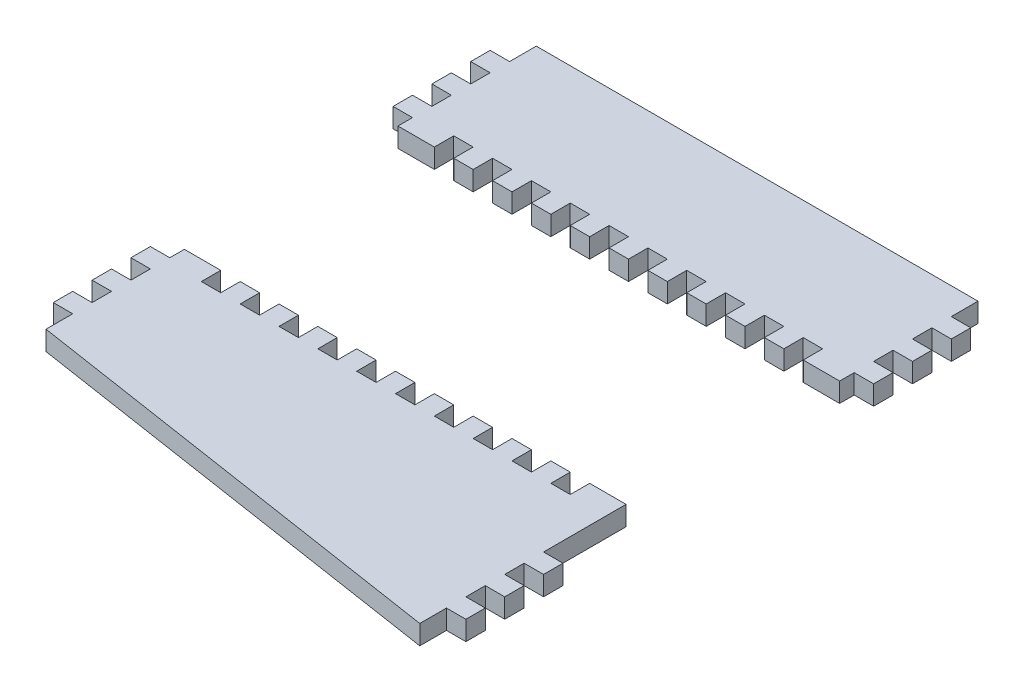
SolidWorks part; units mm, degrees
material "Cedar"
ref_plane "Front Plane" through (0, 0, 0) normal (0, 0, 1) x (1, 0, 0)
ref_plane "Top Plane" through (0, 0, 0) normal (0, 1, 0) x (1, 0, 0)
ref_plane "Right Plane" through (0, 0, 0) normal (1, 0, 0) x (0, 0, -1)
sketch "Sketch1" plane through (0, 0, 0) normal (0, 1, 0) x (1, 0, 0)
  line L0 (-14.4787, 45) -> (-18.4787, 45)
  line L1 (-18.4787, 45) -> (-18.4787, 41)
  line L2 (-18.4787, 41) -> (-14.4787, 41)
  line L3 (-14.4787, 41) -> (-14.4787, 37)
  line L4 (-14.4787, 37) -> (-18.4787, 37)
  line L5 (-18.4787, 37) -> (-18.4787, 33)
  line L6 (-14.4787, 45) -> (-14.4787, 50.5)
  line L7 (-14.4787, 50.5) -> (76.5213, 50.5)
  line L8 (-14.4787, 25) -> (-14.4787, -25)
  line L9 (-14.4787, 33) -> (-18.4787, 33)
  line L10 (-14.4787, 29) -> (-14.4787, 33)
  line L11 (0, 0) -> (-45.8811, 0) construction
  line L12 (-18.4787, 29) -> (-14.4787, 29)
  line L13 (-18.4787, 25) -> (-18.4787, 29)
  line L14 (-14.4787, 25) -> (-18.4787, 25)
  line L15 (-14.4787, 442.2268) -> (-14.4787, 342.2268) construction
  line L16 (-14.4787, 442.2268) -> (1285.5213, 442.2268) construction
  line L17 (-14.4787, 342.2268) -> (1285.5213, 142.2268) construction
  line L18 (1285.5213, 142.2268) -> (1285.5213, 442.2268) construction
  line L19 (-7.4787, 442.2268) -> (-7.4787, 341.1498) construction
  line L20 (96.5213, 442.2268) -> (96.5213, 325.1498) construction
  line L21 (1285.5213, 442.2268) -> (1885.5213, 442.2268) construction
  line L22 (1885.5213, 442.2268) -> (1885.5213, 142.2268) construction
  line L23 (1885.5213, 142.2268) -> (1285.5213, 142.2268) construction
  line L24 (1885.5213, 442.2268) -> (2485.5213, 442.2268) construction
  line L25 (2485.5213, 442.2268) -> (2485.5213, 342.2268) construction
  line L26 (2485.5213, 342.2268) -> (1885.5213, 142.2268) construction
  line L27 (-18.4787, 35) -> (-56.1025, 35) construction
  line L28 (80.5213, 35) -> (126.3703, 35) construction
  line L29 (76.5213, 50.5) -> (76.5213, 45)
  line L30 (76.5213, 45) -> (80.5213, 45)
  line L31 (80.5213, 45) -> (80.5213, 41)
  line L32 (80.5213, 41) -> (76.5213, 41)
  line L33 (76.5213, 41) -> (76.5213, 37)
  line L34 (76.5213, 37) -> (80.5213, 37)
  line L35 (80.5213, 37) -> (80.5213, 33)
  line L36 (80.5213, 33) -> (76.5213, 33)
  line L37 (76.5213, 33) -> (76.5213, 29)
  line L38 (76.5213, 29) -> (80.5213, 29)
  line L39 (80.5213, 29) -> (80.5213, 25)
  line L40 (80.5213, 25) -> (76.5213, 25)
  line L41 (76.5213, 25) -> (76.5213, -39)
  line L42 (10.595, -7) -> (87.8667, -7) construction
  line L43 (-14.4787, -25) -> (-18.4787, -25)
  line L44 (-18.4787, -25) -> (-18.4787, -29)
  line L45 (-18.4787, -29) -> (-14.4787, -29)
  line L46 (-14.4787, -29) -> (-14.4787, -33)
  line L47 (-14.4787, -33) -> (-18.4787, -33)
  line L48 (-14.4787, -45) -> (-14.4787, -50.5)
  line L49 (-18.4787, -37) -> (-18.4787, -33)
  line L50 (-14.4787, -37) -> (-18.4787, -37)
  line L51 (-14.4787, -41) -> (-14.4787, -37)
  line L52 (-18.4787, -41) -> (-14.4787, -41)
  line L53 (-18.4787, -45) -> (-18.4787, -41)
  line L54 (-14.4787, -45) -> (-18.4787, -45)
  line L55 (80.5213, -39) -> (76.5213, -39)
  line L56 (80.5213, -43) -> (80.5213, -39)
  line L57 (76.5213, -43) -> (80.5213, -43)
  line L58 (76.5213, -47) -> (76.5213, -43)
  line L59 (80.5213, -47) -> (76.5213, -47)
  line L60 (80.5213, -51) -> (80.5213, -47)
  line L61 (76.5213, -51) -> (80.5213, -51)
  line L62 (76.5213, -55) -> (76.5213, -51)
  line L63 (80.5213, -55) -> (76.5213, -55)
  line L64 (80.5213, -59) -> (80.5213, -55)
  line L65 (76.5213, -59) -> (80.5213, -59)
  line L66 (76.5213, -64.5) -> (76.5213, -59)
  line L67 (-14.4787, -50.5) -> (76.5213, -64.5)
  line L68 (290.5213, 442.2268) -> (290.5213, 295.3037) construction
  line L69 (615.5213, 442.2268) -> (615.5213, 245.3037) construction
  line L70 (935.5213, 442.2268) -> (935.5213, 196.0729) construction
  line L71 (1485.5213, 442.2268) -> (1485.5213, 142.2268) construction
  line L72 (1685.5213, 442.2268) -> (1685.5213, 142.2268) construction
  line L73 (2187.5213, 442.2268) -> (2187.5213, 242.2268) construction
  line L74 (1285.5213, 896.9349) -> (1285.5213, 1196.9349) construction
  line L75 (1285.5213, 1046.9349) -> (-14.4787, 1046.9349) construction
  line L76 (-14.4787, 1046.9349) -> (-14.4787, 1104.4349) construction
  line L77 (-14.4787, 1104.4349) -> (1285.5213, 1196.9349) construction
  line L78 (-14.4787, 1046.9349) -> (-14.4787, 989.4349) construction
  line L79 (-14.4787, 989.4349) -> (1285.5213, 896.9349) construction
  line L80 (96.5213, 1112.333) -> (96.5213, 981.5369) construction
  line L81 (290.5213, 967.733) -> (290.5213, 1126.1369) construction
  line L82 (615.5213, 1149.2619) -> (615.5213, 944.608) construction
  line L83 (935.5213, 921.8388) -> (935.5213, 1172.0311) construction
  line L84 (-3.4787, 442.2268) -> (-3.4787, 340.5345) construction
  line L85 (100.5213, 442.2268) -> (100.5213, 324.5345) construction
  line L86 (294.5213, 442.2268) -> (294.5213, 294.6883) construction
  line L87 (619.5213, 442.2268) -> (619.5213, 244.6883) construction
  line L88 (939.5213, 442.2268) -> (939.5213, 195.4575) construction
  line L89 (1881.5213, 442.2268) -> (1881.5213, 142.2268) construction
  line L90 (1289.5213, 442.2268) -> (1289.5213, 142.2268) construction
  line L91 (1489.5213, 442.2268) -> (1489.5213, 142.2268) construction
  line L92 (1689.5213, 442.2268) -> (1689.5213, 142.2268) construction
  line L93 (1285.5213, 1196.9349) -> (1885.5213, 1196.9349) construction
  line L94 (1885.5213, 1196.9349) -> (1885.5213, 896.9349) construction
  line L95 (1885.5213, 896.9349) -> (1285.5213, 896.9349) construction
  line L96 (1885.5213, 1196.9349) -> (2485.5213, 1052.9349) construction
  line L97 (2485.5213, 1052.9349) -> (2485.5213, 1040.9349) construction
  line L98 (2485.5213, 1040.9349) -> (1885.5213, 896.9349) construction
  line L99 (2191.5213, 1123.4949) -> (2191.5213, 970.3749) construction
  line L100 (2191.5213, 442.2268) -> (2191.5213, 244.2268) construction
  line L101 (2481.5213, 442.2268) -> (2481.5213, 340.8934) construction
  line L102 (-7.4787, 1104.933) -> (-7.4787, 988.9369) construction
  text T0 "Vedere laterala"
  text T1 "vedere laterala" font "Century Gothic" height in points 28
  point P50 (-14.4787, 0)
  point P63 (76.5213, -7)
  dimension "D2" = 4
  dimension "D3" = 4
  dimension "D4" = 4
  dimension "D5" = 4
  dimension "D6" = 91
  dimension "D7" = 100
  dimension "D8" = 346
  dimension "D9" = 300
  dimension "D10" = 115.9962
  dimension "D11" = 7
  dimension "D12" = 100
  dimension "D13" = 4
  dimension "D14" = 290
  dimension "D15" = 101.0769
  dimension "D16" = 117.0769
  dimension "D17" = 35
  dimension "D18" = 50.5
  dimension "D19" = 4
  dimension "D20" = 4
  dimension "D21" = 15.5
  dimension "D22" = 4
  dimension "D23" = 4
  dimension "D24" = 4
  dimension "D25" = 4
  dimension "D26" = 4
  dimension "D27" = 7
  dimension "D28" = 4
  dimension "D29" = 100
  dimension "D30" = 4
  dimension "D31" = 146.9231
  dimension "D32" = 4
  dimension "D33" = 4
  dimension "D34" = 196.9231
  dimension "D35" = 246.1538
  dimension "D36" = 4
  dimension "D37" = 196
  dimension "D38" = 302
  dimension "D39" = 198
  dimension "D40" = 300
  dimension "D41" = 57.5
  dimension "D42" = 57.5
  dimension "D43" = 130.7962
  dimension "D44" = 158.4038
  dimension "D45" = 204.6538
  dimension "D46" = 250.1923
  dimension "D47" = 4
  dimension "D48" = 190
  dimension "D49" = 321
  dimension "D50" = 104
  dimension "D51" = 4
  dimension "D52" = 4
  dimension "D53" = 196
  dimension "D54" = 4
  dimension "D55" = 192
  dimension "D56" = 600
  dimension "D57" = 1300
  dimension "D58" = 6
  dimension "D59" = 6
  dimension "D60" = 4
  dimension "D61" = 4
  dimension "D62" = 600
  dimension "D63" = 300
  dimension "D64" = 153.12
  dimension "D65" = 194
  dimension "D66" = 325
  dimension "D67" = 320
  dimension "D68" = 350
  dimension "D69" = 316
extrude "Boss-Extrude1" add sketch "Sketch1" along normal blind 4 contours L67 L66 L65 L64 L63 L62 L61 L60 L59 L58 L57 L56 L55 L41 L40 L39 L38 L37 L36 L35 L34 L33 L32 L31 L30 L29 L7 L6 L0 L1 L2 L3 L4 L5 L9 L10 L12 L13 L14 L8 L43 L44 L45 L46 L47 L49 L50 L51 L52 L53 L54 L48
sketch "Sketch4" plane through (0, 4, 0) normal (0, 1, 0) x (1, 0, 0)
  line L0 (-34.2055, 0) -> (100.0971, 0) construction
  line L1 (-30.6838, -22) -> (110.8948, -22)
  line L2 (110.8948, -22) -> (110.8948, 22)
  line L3 (110.8948, 22) -> (-30.6838, 22)
  line L4 (-30.6838, 22) -> (-30.6838, -22)
  dimension "D1" = 22
  dimension "D2" = 22
extrude "Cut-Extrude1" cut sketch "Sketch4" against normal blind 4
sketch "Sketch5" plane through (0, 4, 0) normal (0, 1, 0) x (1, 0, 0)
  line L0 (-14.4787, 50.5) -> (76.5213, 50.5) construction
  line L1 (31.0213, 50.5) -> (31.0213, -65.3136) construction
  line L2 (29.0213, 22) -> (33.0213, 22)
  line L3 (76.5213, 22) -> (-14.4787, 22) construction
  line L4 (33.0213, 22) -> (33.0213, 26)
  line L5 (33.0213, 26) -> (37.0213, 26)
  line L6 (37.0213, 26) -> (37.0213, 22)
  line L7 (37.0213, 22) -> (41.0213, 22)
  line L8 (41.0213, 22) -> (41.0213, 23.461)
  line L9 (41.0213, 22) -> (41.0213, 26)
  line L10 (41.0213, 26) -> (45.0213, 26)
  line L11 (45.0213, 26) -> (45.0213, 22)
  line L12 (45.0213, 22) -> (49.0213, 22)
  line L13 (49.0213, 22) -> (49.0213, 23.461)
  line L14 (49.0213, 22) -> (49.0213, 26)
  line L15 (49.0213, 26) -> (53.0213, 26)
  line L16 (53.0213, 26) -> (53.0213, 22)
  line L17 (53.0213, 22) -> (57.0213, 22)
  line L18 (57.0213, 22) -> (57.0213, 23.461)
  line L19 (57.0213, 22) -> (57.0213, 26)
  line L20 (57.0213, 26) -> (61.0213, 26)
  line L21 (61.0213, 26) -> (61.0213, 22)
  line L22 (61.0213, 22) -> (65.0213, 22)
  line L23 (65.0213, 22) -> (65.0213, 23.461)
  line L24 (65.0213, 22) -> (65.0213, 26)
  line L25 (65.0213, 26) -> (69.0213, 26)
  line L26 (69.0213, 26) -> (69.0213, 22)
  line L27 (69.0213, 22) -> (73.0213, 22)
  line L28 (73.0213, 22) -> (73.0213, 13.939)
  line L29 (73.0213, 22) -> (73.0213, 23.461) [skipped]
  line L30 (73.0213, 13.939) -> (-10.9787, 13.939)
  line L31 (-10.9787, 22) -> (-10.9787, 13.939)
  line L32 (-6.9787, 22) -> (-10.9787, 22)
  line L33 (-6.9787, 26) -> (-6.9787, 22)
  line L34 (-2.9787, 26) -> (-6.9787, 26)
  line L35 (-2.9787, 22) -> (-2.9787, 26)
  line L36 (-2.9787, 22) -> (-2.9787, 23.461)
  line L37 (1.0213, 22) -> (-2.9787, 22)
  line L38 (1.0213, 26) -> (1.0213, 22)
  line L39 (5.0213, 26) -> (1.0213, 26)
  line L40 (5.0213, 22) -> (5.0213, 26)
  line L41 (5.0213, 22) -> (5.0213, 23.461)
  line L42 (9.0213, 22) -> (5.0213, 22)
  line L43 (9.0213, 26) -> (9.0213, 22)
  line L44 (13.0213, 26) -> (9.0213, 26)
  line L45 (13.0213, 22) -> (13.0213, 26)
  line L46 (13.0213, 22) -> (13.0213, 23.461)
  line L47 (17.0213, 22) -> (13.0213, 22)
  line L48 (17.0213, 26) -> (17.0213, 22)
  line L49 (21.0213, 26) -> (17.0213, 26)
  line L50 (21.0213, 22) -> (21.0213, 26)
  line L51 (21.0213, 22) -> (21.0213, 23.461)
  line L52 (25.0213, 22) -> (21.0213, 22)
  line L53 (25.0213, 26) -> (25.0213, 22)
  line L54 (29.0213, 26) -> (25.0213, 26)
  line L55 (29.0213, 22) -> (29.0213, 26)
  line L56 (-14.4787, 22) -> (-14.4787, -22) construction
  line L57 (-14.4787, 0) -> (80.1451, 0) construction
  line L58 (29.0213, -22) -> (29.0213, -26)
  line L59 (29.0213, -26) -> (25.0213, -26)
  line L60 (25.0213, -26) -> (25.0213, -22)
  line L61 (25.0213, -22) -> (21.0213, -22)
  line L62 (21.0213, -22) -> (21.0213, -23.461)
  line L63 (21.0213, -22) -> (21.0213, -26)
  line L64 (21.0213, -26) -> (17.0213, -26)
  line L65 (17.0213, -26) -> (17.0213, -22)
  line L66 (17.0213, -22) -> (13.0213, -22)
  line L67 (13.0213, -22) -> (13.0213, -23.461)
  line L68 (13.0213, -22) -> (13.0213, -26)
  line L69 (13.0213, -26) -> (9.0213, -26)
  line L70 (9.0213, -26) -> (9.0213, -22)
  line L71 (9.0213, -22) -> (5.0213, -22)
  line L72 (5.0213, -22) -> (5.0213, -23.461)
  line L73 (5.0213, -22) -> (5.0213, -26)
  line L74 (5.0213, -26) -> (1.0213, -26)
  line L75 (1.0213, -26) -> (1.0213, -22)
  line L76 (1.0213, -22) -> (-2.9787, -22)
  line L77 (-2.9787, -22) -> (-2.9787, -23.461)
  line L78 (-2.9787, -22) -> (-2.9787, -26)
  line L79 (-2.9787, -26) -> (-6.9787, -26)
  line L80 (-6.9787, -26) -> (-6.9787, -22)
  line L81 (-6.9787, -22) -> (-10.9787, -22)
  line L82 (-10.9787, -22) -> (-10.9787, -13.939)
  line L83 (73.0213, -13.939) -> (-10.9787, -13.939)
  line L84 (73.0213, -22) -> (73.0213, -13.939)
  line L85 (69.0213, -22) -> (73.0213, -22)
  line L86 (69.0213, -26) -> (69.0213, -22)
  line L87 (65.0213, -26) -> (69.0213, -26)
  line L88 (65.0213, -22) -> (65.0213, -26)
  line L89 (65.0213, -22) -> (65.0213, -23.461)
  line L90 (61.0213, -22) -> (65.0213, -22)
  line L91 (61.0213, -26) -> (61.0213, -22)
  line L92 (57.0213, -26) -> (61.0213, -26)
  line L93 (57.0213, -22) -> (57.0213, -26)
  line L94 (57.0213, -22) -> (57.0213, -23.461)
  line L95 (53.0213, -22) -> (57.0213, -22)
  line L96 (53.0213, -26) -> (53.0213, -22)
  line L97 (49.0213, -26) -> (53.0213, -26)
  line L98 (49.0213, -22) -> (49.0213, -26)
  line L99 (49.0213, -22) -> (49.0213, -23.461)
  line L100 (45.0213, -22) -> (49.0213, -22)
  line L101 (45.0213, -26) -> (45.0213, -22)
  line L102 (41.0213, -26) -> (45.0213, -26)
  line L103 (41.0213, -22) -> (41.0213, -26)
  line L104 (41.0213, -22) -> (41.0213, -23.461)
  line L105 (37.0213, -22) -> (41.0213, -22)
  line L106 (37.0213, -26) -> (37.0213, -22)
  line L107 (33.0213, -26) -> (37.0213, -26)
  line L108 (33.0213, -22) -> (33.0213, -26)
  line L109 (29.0213, -22) -> (33.0213, -22)
  point P43 (31.0213, 13.939)
  point P126 (31.0213, -13.939)
  dimension "D1" = 2
  dimension "D2" = 4
  dimension "D3" = 4
  dimension "D4" = 4
  dimension "D6" = 24.5
  dimension "D5" = 5
extrude "Cut-Extrude3" cut sketch "Sketch5" against normal blind 4 contours L1 L31 L30 L28 | L58 L109 L108 L107 L106 L105 L103 L102 L101 L100 L98 L97 L96 L95 L93 L92 L91 L90 L88 L87 L86 L85 L84 L83 L82 L81 L80 L79 L78 L77 L76 L75 L74 L73 L72 L71 L70 L69 L68 L67 L66 L65 L64 L63 L62 L61 L60 | L1 L35 L34 L33 | L1 L40 L39 L38 | L1 L45 L44 L43 | L1 L50 L49 L48 | L1 L55 L54 L53 | L6 L5 L4 L1 | L11 L10 L9 L8 L1 | L16 L15 L14 L13 L1 | L21 L20 L19 L18 L1 | L26 L25 L24 L23 L1
